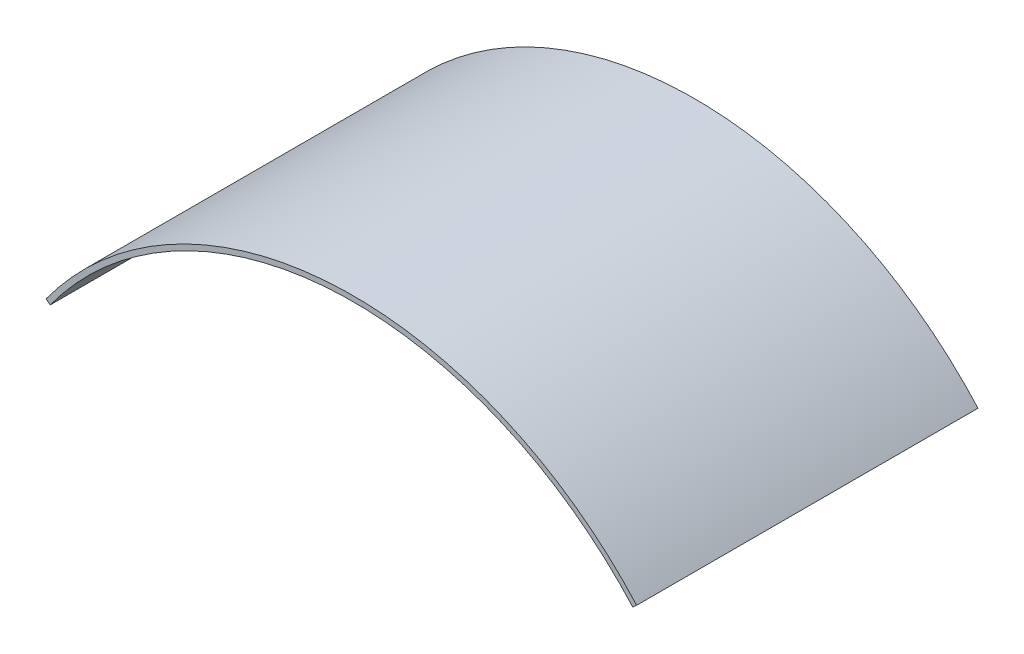
SolidWorks part; units mm, degrees
ref_plane "Front Plane" through (0, 0, 0) normal (0, 0, 1) x (1, 0, 0)
ref_plane "Top Plane" through (0, 0, 0) normal (0, 1, 0) x (1, 0, 0)
ref_plane "Right Plane" through (0, 0, 0) normal (1, 0, 0) x (0, 0, -1)
sketch "Sketch1" plane through (0, 0, 0) normal (0, 0, 1) x (1, 0, 0)
  line L0 (0, 0) -> (1.4143, -1.0306)
  line L1 (196.4044, 9.9646) -> (195.1016, 8.7961)
  arc A0 (0, 0) -> (196.4044, 9.9646) centre (102.2347, -74.4997) cw
  arc A1 (1.4143, -1.0306) -> (195.1016, 8.7961) centre (102.2347, -74.4997) cw
  arc A2 (0, 0) -> (196.4044, 9.9646) centre (102.2347, -74.4997) cw construction
  dimension "D2" = 126.4996
  dimension "D3" = 195.1016
  dimension "D1" = 1.75
extrude "Boss-Extrude1" add sketch "Sketch1" along normal blind 113.5
